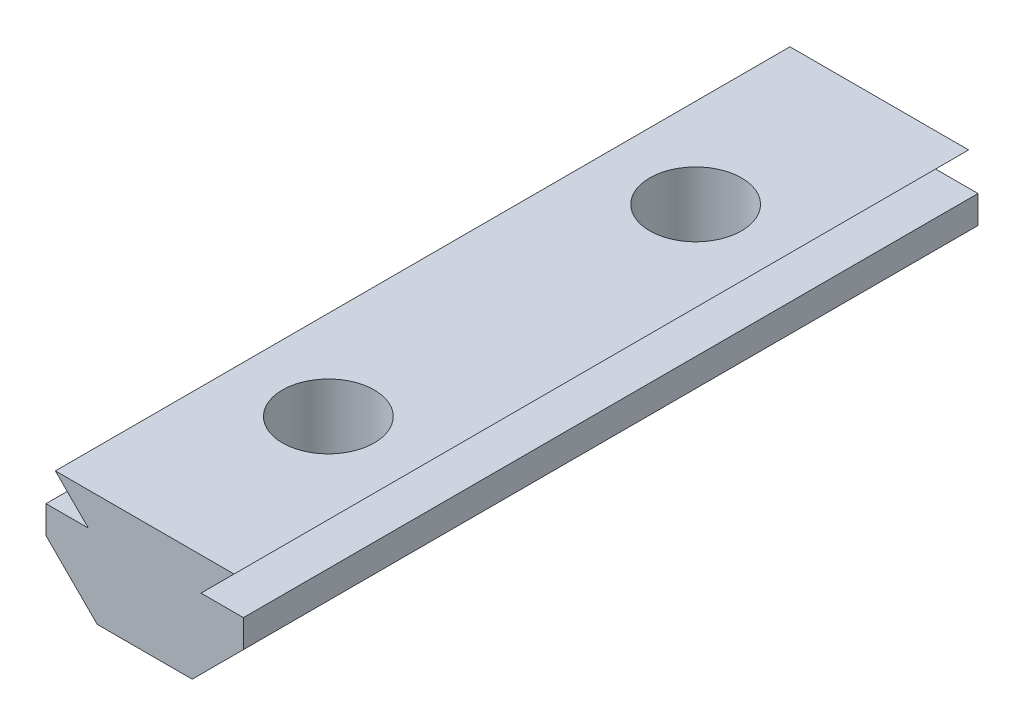
SolidWorks part; units mm, degrees
ref_plane "Front Plane" through (0, 0, 0) normal (0, 0, 1) x (1, 0, 0)
ref_plane "Top Plane" through (0, 0, 0) normal (0, 1, 0) x (1, 0, 0)
ref_plane "Right Plane" through (0, 0, 0) normal (1, 0, 0) x (0, 0, -1)
sketch "Sketch1" plane through (0, 0, 0) normal (0, 0, 1) x (1, 0, 0)
  line L0 (-2.5857, 0) -> (2.5857, 0)
  line L1 (2.5857, 0) -> (5.375, 2.7893)
  line L2 (-2.5857, 0) -> (-5.375, 2.7893)
  line L3 (-5.375, 2.7893) -> (-5.375, 4.3)
  line L4 (5.375, 2.7893) -> (5.375, 4.3)
  line L5 (-5.375, 4.3) -> (-3.065, 4.3)
  line L6 (5.375, 4.3) -> (3.065, 4.3)
  line L7 (-3.065, 4.3) -> (-4.865, 6.1)
  line L8 (3.065, 4.3) -> (4.865, 6.1)
  line L9 (4.865, 6.1) -> (-4.865, 6.1)
  point P4 (0, 0)
  dimension "D1" = 6.13
  dimension "D2" = 10.75
  dimension "D3" = 4.3
  dimension "D4" = 4.3
  dimension "D5" = 1.8
  dimension "D6" = 1.8
extrude "Boss-Extrude1" add sketch "Sketch1" along normal blind 40
sketch "Sketch2" plane through (0, 6.1, 0) normal (0, 1, 0) x (1, 0, 0)
  line L0 (0, 0) -> (0, -40) construction
  line L1 (4.865, 0) -> (-4.865, 0) construction
  line L2 (4.865, -40) -> (-4.865, -40) construction
  circle A0 centre (0, -30) radius 2.5
  circle A1 centre (0, -10) radius 2.5
  dimension "D3" = 5
  dimension "D1" = 10
  dimension "D2" = 10
extrude "Cut-Extrude1" cut sketch "Sketch2" against normal through all
